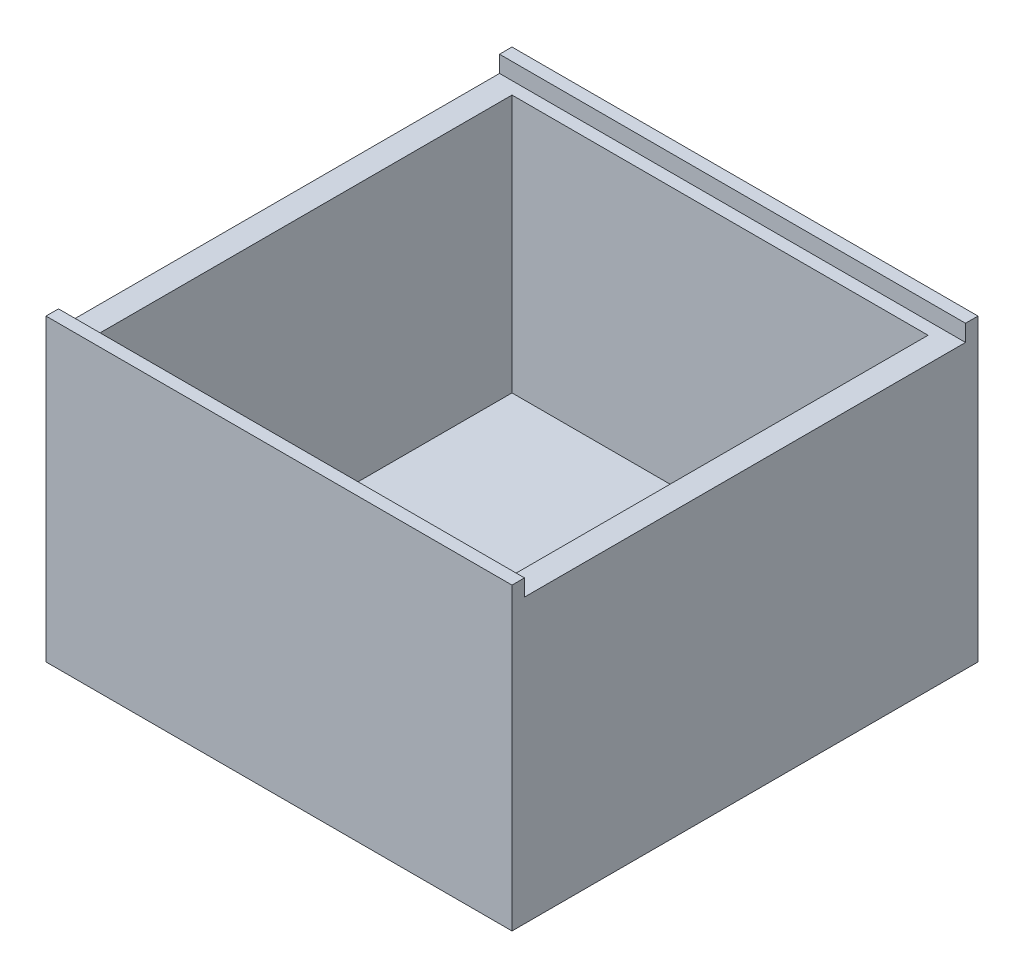
SolidWorks part; units mm, degrees
ref_plane "Front Plane" through (0, 0, 0) normal (0, 0, 1) x (1, 0, 0)
ref_plane "Top Plane" through (0, 0, 0) normal (0, 1, 0) x (1, 0, 0)
ref_plane "Right Plane" through (0, 0, 0) normal (1, 0, 0) x (0, 0, -1)
sketch "Sketch1" plane through (0, 0, 0) normal (0, 1, 0) x (1, 0, 0)
  line L0 (-36.9903, 0) -> (40.6586, 0) construction
  line L1 (-14, 14) -> (14, 14)
  line L2 (-14, 14) -> (-14, -14)
  line L3 (-14, -14) -> (14, -14)
  line L4 (14, 14) -> (14, -14)
  line L5 (0, 23.8774) -> (0, -23.0662) construction
  dimension "D1" = 28
  dimension "D2" = 28
extrude "Boss-Extrude1" add sketch "Sketch1" along normal blind 18
shell "Shell2" thickness 1.5
sketch "Sketch2" plane through (-14, 0, 0) normal (-1, 0, 0) x (0, 0, 1)
  line L0 (-13.25, 18) -> (-13.25, 17)
  line L1 (-14, 18) -> (14, 18) construction
  line L2 (-13.25, 17) -> (13.25, 17)
  line L3 (13.25, 17) -> (13.25, 18)
  line L4 (13.25, 18) -> (-13.25, 18)
  line L5 (0, 0) -> (0, 18.9192) construction
  line L6 (-14, 0) -> (14, 0) construction
  dimension "D1" = 26.5
  dimension "D2" = 1
extrude "Cut-Extrude1" cut sketch "Sketch2" against normal through all
